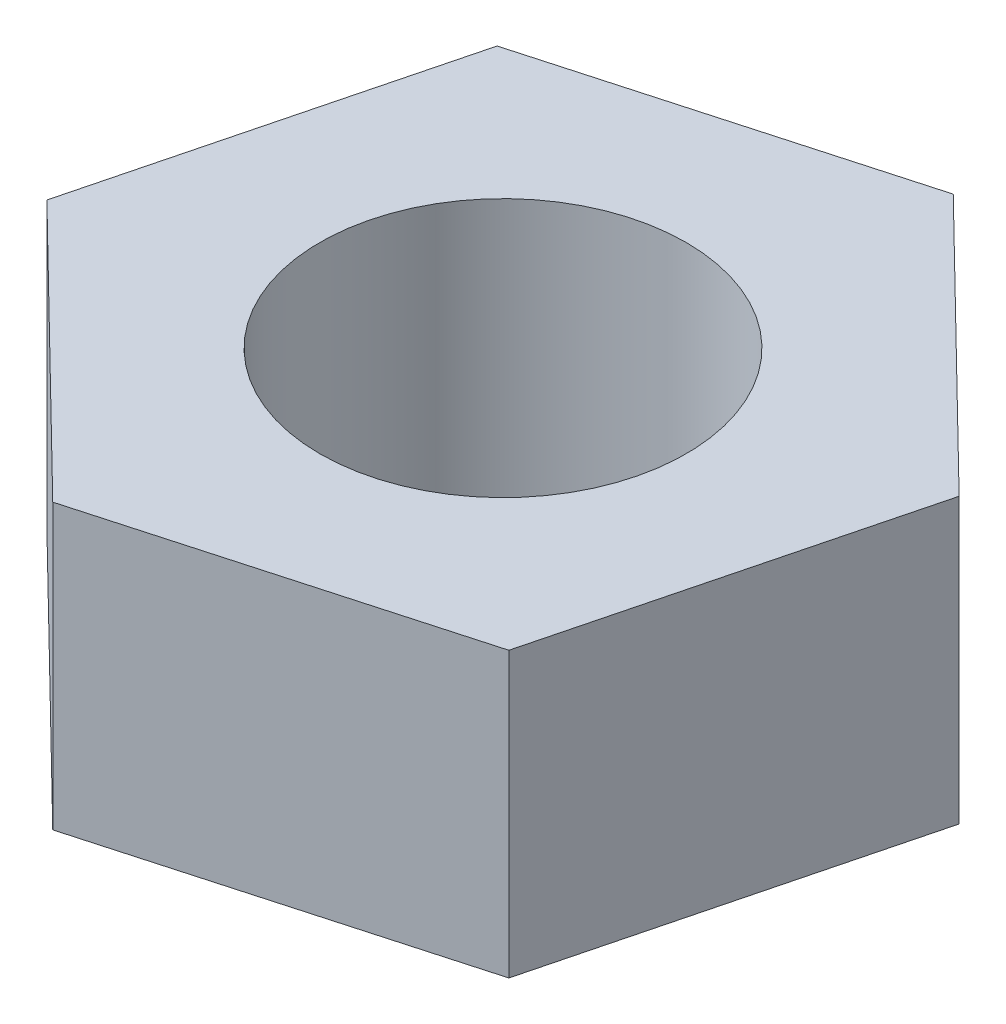
SolidWorks part; units mm, degrees
ref_plane "前视基准面" through (0, 0, 0) normal (0, 0, 1) x (1, 0, 0)
ref_plane "上视基准面" through (0, 0, 0) normal (0, 1, 0) x (1, 0, 0)
ref_plane "右视基准面" through (0, 0, 0) normal (1, 0, 0) x (0, 0, -1)
sketch "草图1" plane through (0, 0, 0) normal (0, 1, 0) x (1, 0, 0)
  line L1 (2.8897, -2.8255) -> (3.8917, 1.0898)
  line L2 (3.8917, 1.0898) -> (1.0021, 3.9152)
  line L3 (1.0021, 3.9152) -> (-2.8897, 2.8255)
  line L4 (-2.8897, 2.8255) -> (-3.8917, -1.0898)
  line L5 (-3.8917, -1.0898) -> (-1.0021, -3.9152)
  line L6 (-1.0021, -3.9152) -> (2.8897, -2.8255)
  circle A0 centre (0, 0) radius 2
  circle A1 centre (0, 0) radius 3.5 construction
  dimension "D1" = 4
  dimension "D2" = 7
extrude "凸台-拉伸1" add sketch "草图1" along normal blind 3.1
